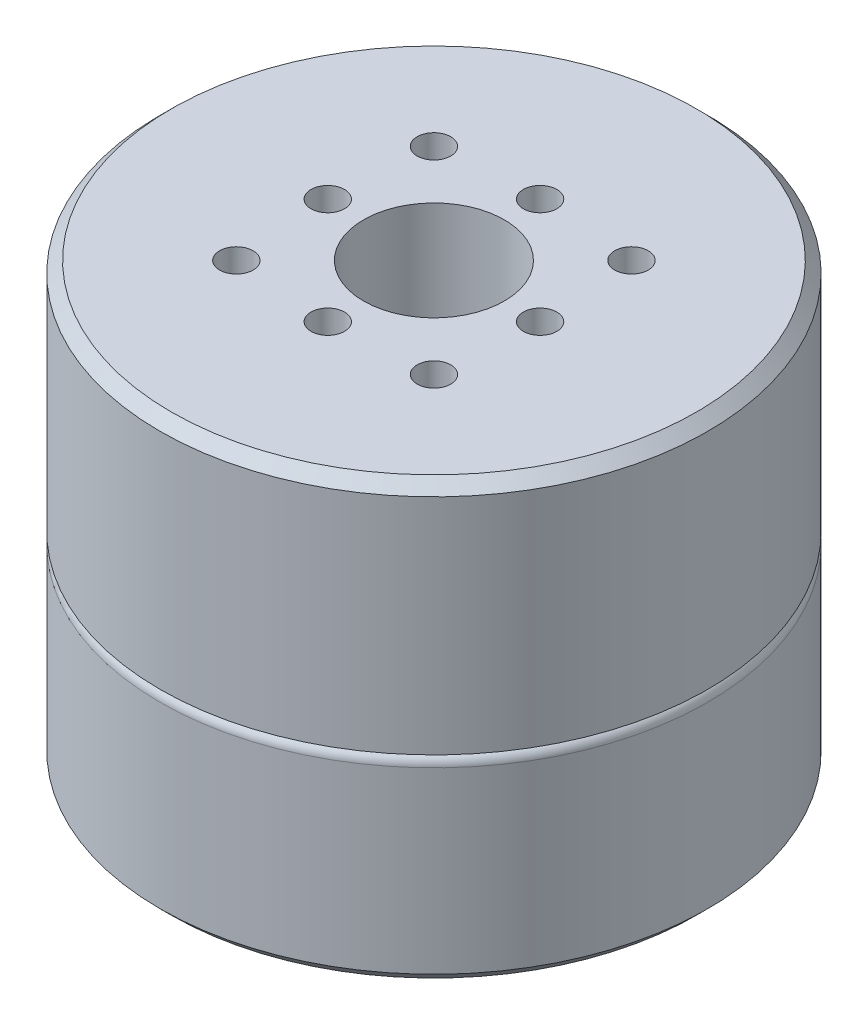
SolidWorks part; units mm, degrees
material "1060 合金"
ref_plane "前视基准面" through (0, 0, 0) normal (0, 0, 1) x (1, 0, 0)
ref_plane "上视基准面" through (0, 0, 0) normal (0, 1, 0) x (1, 0, 0)
ref_plane "右视基准面" through (0, 0, 0) normal (1, 0, 0) x (0, 0, -1)
sketch "草图1" plane through (0, 0, 0) normal (0, 1, 0) x (1, 0, 0)
  circle A0 centre (0, 0) radius 24.5
  dimension "D1" = 49
extrude "凸台-拉伸1" add sketch "草图1" along normal blind 18
fillet "圆角1" radius 1 1 edges at (0, 18, 24.5)
sketch "草图2" plane through (0, 18, 0) normal (0, 1, 0) x (1, 0, 0)
  circle A0 centre (0, 0) radius 24.5
extrude "凸台-拉伸2" add sketch "草图2" along normal blind 21
chamfer "倒角1" distance 1 angle 45 1 edges at (0, 39, 24.5)
chamfer "倒角2" distance 1 angle 45 1 edges at (0, 0, 24.5)
sketch "草图4" plane through (0, 39, 0) normal (0, 1, 0) x (1, 0, 0)
  circle A0 centre (0, 0) radius 6.3
  dimension "D1" = 12.6
extrude "切除-拉伸1" cut sketch "草图4" against normal blind 10
sketch "草图5" plane through (0, 39, 0) normal (0, 1, 0) x (1, 0, 0)
  line L0 (0, 9.5) -> (0, -9.5) construction
  line L1 (9.5, 0) -> (-9.5, 0) construction
  line L2 (0, 0) -> (13.5621, 13.5621) construction
  circle A0 centre (0, 0) radius 9.5 construction
  circle A1 centre (9.5, 0) radius 1.5
  circle A2 centre (0, -9.5) radius 1.5
  circle A3 centre (-9.5, 0) radius 1.5
  circle A4 centre (0, 9.5) radius 1.5
  circle A5 centre (0, 0) radius 12.5 construction
  circle A6 centre (8.8388, 8.8388) radius 1.5
  circle A7 centre (8.8388, -8.8388) radius 1.5
  circle A8 centre (-8.8388, -8.8388) radius 1.5
  circle A9 centre (-8.8388, 8.8388) radius 1.5
  dimension "D1" = 19
  dimension "D2" = 3
  dimension "D4" = 25
  dimension "D5" = 3
  dimension "D3" = 4
  dimension "D6" = 4
extrude "切除-拉伸2" cut sketch "草图5" against normal blind 5
sketch "草图6" plane through (0, 0, 0) normal (0, -1, 0) x (1, 0, 0)
  line L0 (0, 0) -> (15, 0) construction
  circle A0 centre (0, 0) radius 15 construction
  circle A1 centre (15, 0) radius 1.5
  circle A2 centre (0, -15) radius 1.5
  circle A3 centre (-15, 0) radius 1.5
  circle A4 centre (0, 15) radius 1.5
  dimension "D1" = 30
  dimension "D2" = 3
  dimension "D3" = 4
extrude "切除-拉伸3" cut sketch "草图6" against normal blind 5
sketch "草图7" plane through (0, 0, 0) normal (0, 0, 1) x (1, 0, 0)
  line L0 (0, -21.3273) -> (0, 94.7432) construction
